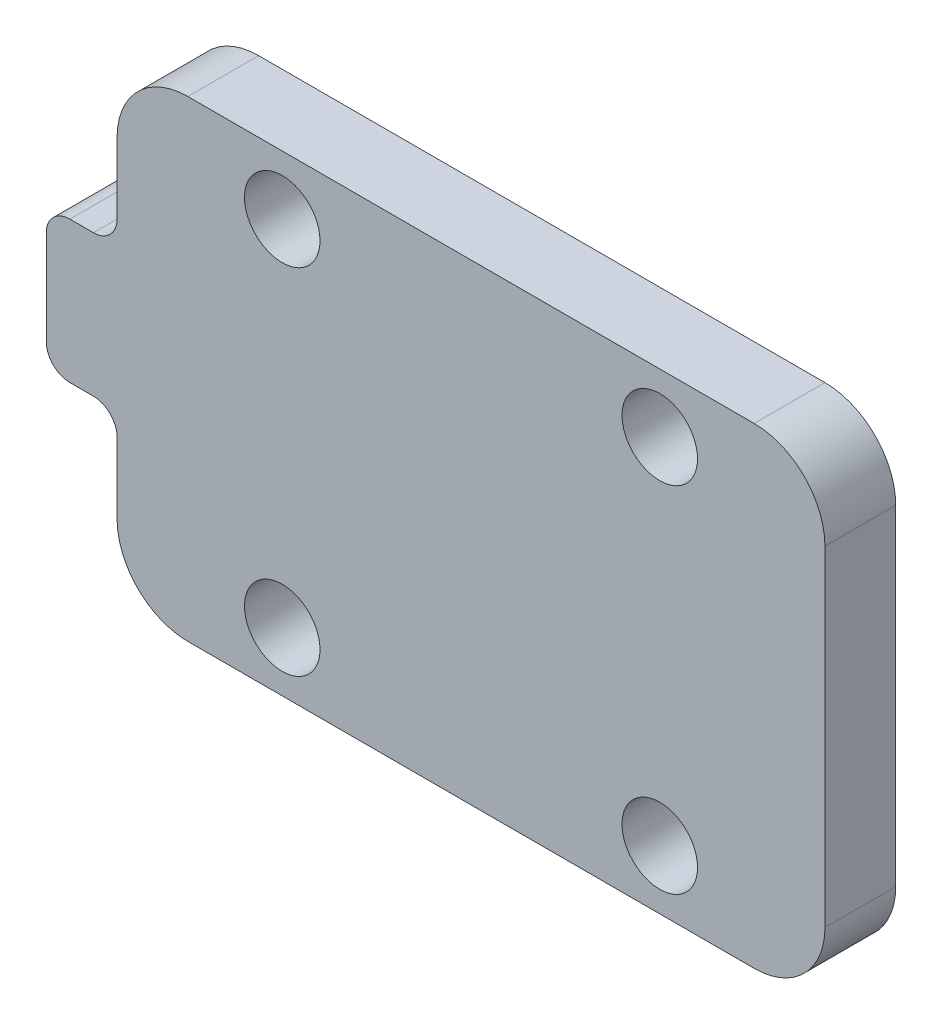
SolidWorks part; units mm, degrees
ref_plane "前视基准面" through (0, 0, 0) normal (0, 0, 1) x (1, 0, 0)
ref_plane "上视基准面" through (0, 0, 0) normal (0, 1, 0) x (1, 0, 0)
ref_plane "右视基准面" through (0, 0, 0) normal (1, 0, 0) x (0, 0, -1)
sketch "草图2" plane through (0, 0, 0) normal (0, 0, 1) x (1, 0, 0)
  line L0 (0, 0) -> (30, 0)
  line L1 (30, 0) -> (30, -20)
  line L2 (30, -20) -> (0, -20)
  line L3 (0, -20) -> (0, 0)
extrude "凸台-拉伸1" add sketch "草图2" along normal blind 3
fillet "圆角1" radius 3 4 edges at (0, 0, 1.5) (0, -20, 1.5) (30, -20, 1.5) (30, 0, 1.5)
sketch "草图3" plane through (0, 0, 3) normal (0, 0, 1) x (1, 0, 0)
  circle A0 centre (23, -2.5) radius 1.6
  circle A1 centre (23, -17.5) radius 1.6
  circle A2 centre (7, -17.5) radius 1.6
  circle A3 centre (7, -2.5) radius 1.6
  dimension "D1" = 3.2
  dimension "D2" = 3.2
  dimension "D3" = 3.2
  dimension "D4" = 3.2
extrude "切除-拉伸1" cut sketch "草图3" against normal through all
sketch "草图4" plane through (0, 0, 0) normal (0, 0, -1) x (-1, 0, 0)
  line L0 (0, -10) -> (0, -13)
  line L2 (0, -3) -> (0, -17) construction
  line L3 (0, -10) -> (0, -7)
  line L4 (0, -7) -> (3, -7)
  line L5 (3, -7) -> (3, -13)
  line L6 (3, -13) -> (0, -13)
extrude "凸台-拉伸2" add sketch "草图4" against normal blind 3
fillet "圆角2" radius 1 4 edges at (0, -7, 1.5) (-3, -7, 1.5) (-3, -13, 1.5) (0, -13, 1.5)
